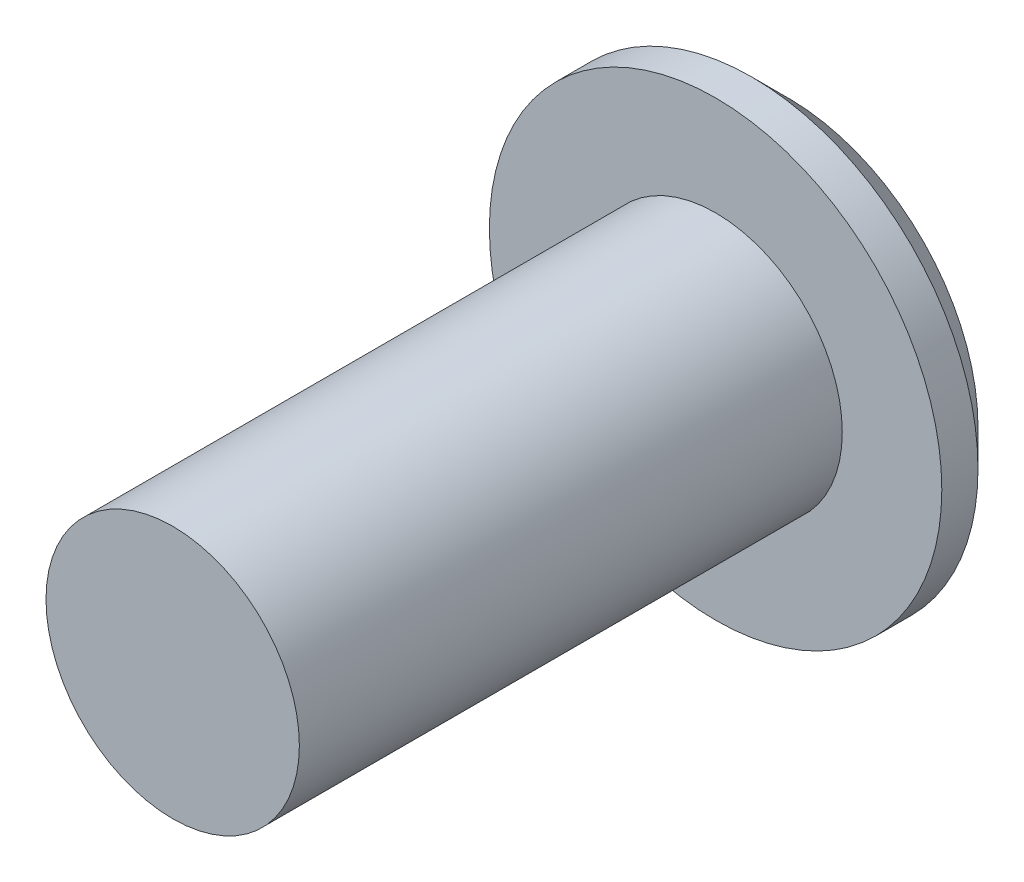
SolidWorks part; units mm, degrees
ref_plane "Front Plane" through (0, 0, 0) normal (0, 0, 1) x (1, 0, 0)
ref_plane "Top Plane" through (0, 0, 0) normal (0, 1, 0) x (1, 0, 0)
ref_plane "Right Plane" through (0, 0, 0) normal (1, 0, 0) x (0, 0, -1)
sketch "Sketch1" plane through (0, 0, 0) normal (0, 0, 1) x (1, 0, 0)
  circle A0 centre (0, 0) radius 12.5
  dimension "D1" = 25
extrude "Boss-Extrude1" add sketch "Sketch1" along normal blind 4
sketch "Sketch2" plane through (0, 0, 4) normal (0, 0, 1) x (1, 0, 0)
  circle A0 centre (0, 0) radius 7
  dimension "D1" = 14
extrude "Boss-Extrude2" add sketch "Sketch2" along normal blind 30
chamfer "Chamfer1" distance 2 angle 45 1 edges at (12.5, 0, 0)
